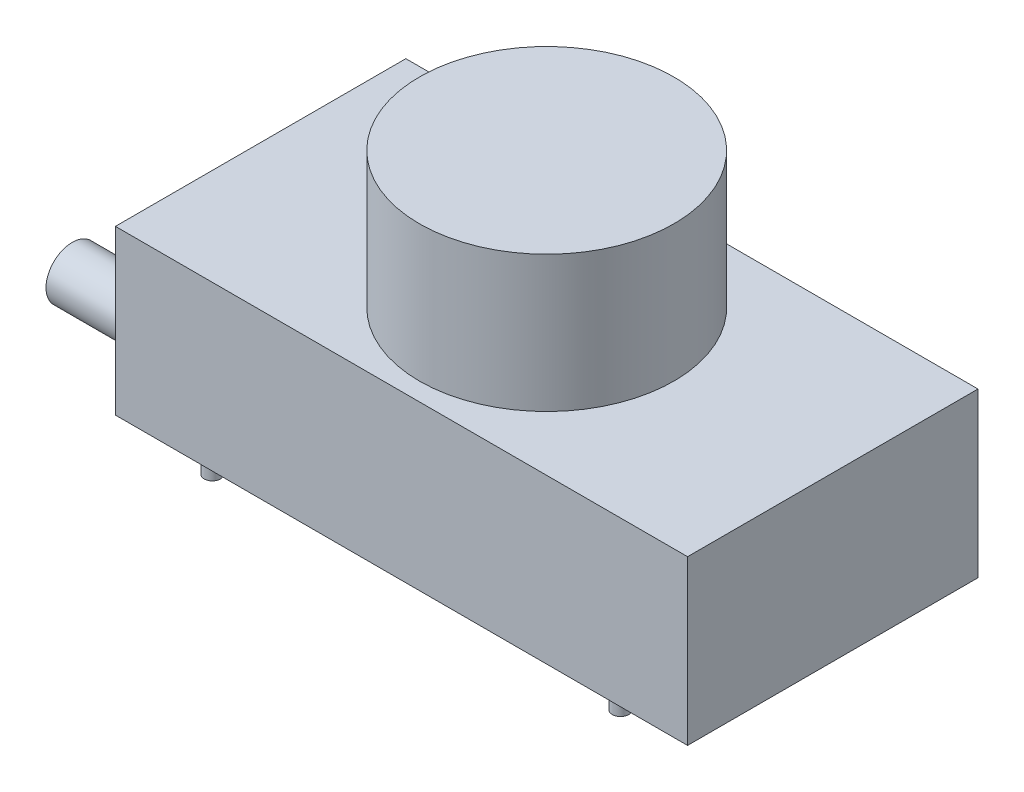
SolidWorks part; units mm, degrees
ref_plane "Front Plane" through (0, 0, 0) normal (0, 0, 1) x (1, 0, 0)
ref_plane "Top Plane" through (0, 0, 0) normal (0, 1, 0) x (1, 0, 0)
ref_plane "Right Plane" through (0, 0, 0) normal (1, 0, 0) x (0, 0, -1)
sketch "Sketch1" plane through (0, 0, 0) normal (0, 1, 0) x (1, 0, 0)
  line L1 (-52.5, -26.65) -> (52.5, -26.65)
  line L2 (-52.5, -26.65) -> (-52.5, 26.65)
  line L3 (-52.5, 26.65) -> (52.5, 26.65)
  line L4 (52.5, -26.65) -> (52.5, 26.65)
  line L5 (-52.5, -26.65) -> (52.5, 26.65) construction
  line L6 (-52.5, 26.65) -> (52.5, -26.65) construction
  point P0 (0, 0)
  dimension "D1" = 105
  dimension "D2" = 53.3
extrude "Boss-Extrude1" add sketch "Sketch1" along normal blind 30
sketch "Sketch2" plane through (-52.5, 0, 0) normal (-1, 0, 0) x (0, 0, 1)
  line L1 (-21.6019, 1.5708) -> (-14.012, 1.5708)
  line L2 (-21.6019, 1.5708) -> (-21.6019, 8.8239)
  line L3 (-21.6019, 8.8239) -> (-14.012, 8.8239)
  line L4 (-14.012, 1.5708) -> (-14.012, 8.8239)
  line L5 (-21.6019, 1.5708) -> (-14.012, 8.8239) construction
  line L6 (-21.6019, 8.8239) -> (-14.012, 1.5708) construction
  circle A0 centre (14.5675, 6.6027) radius 4.8187
  point P0 (-17.807, 5.1974)
extrude "Boss-Extrude2" add sketch "Sketch2" along normal blind 20
sketch "Sketch3" plane through (0, 30, 0) normal (0, 1, 0) x (1, 0, 0)
  circle A0 centre (0, 0) radius 23.3495
extrude "Boss-Extrude3" add sketch "Sketch3" along normal blind 25
sketch "Sketch4" plane through (0, 0, 0) normal (0, -1, 0) x (1, 0, 0)
  line L0 (52.5, -26.65) -> (-52.5, -26.65) construction
  line L1 (-38.5, -24.15) -> (43.6, -24.15) construction
  line L2 (-38.5, -24.15) -> (-38.5, 24.15) construction
  line L3 (-38.5, 24.15) -> (43.6, 24.15) construction
  line L4 (43.6, -24.15) -> (43.6, 24.15) construction
  line L5 (-52.5, 26.65) -> (52.5, 26.65) construction
  line L7 (-52.5, -26.65) -> (-52.5, 26.65) construction
  circle A0 centre (-37.2, 24.15) radius 1.5
  circle A1 centre (-38.5, -24.15) radius 1.5
  circle A2 centre (37.7, 24.15) radius 1.5
  circle A3 centre (43.6, -24.15) radius 1.5
  point P14 (44.7869, -24.15)
  point P15 (40.8602, 24.15)
  dimension "D6" = 3
  dimension "D1" = 2.5
  dimension "D2" = 2.5
  dimension "D3" = 1.3
  dimension "D4" = 74.9
  dimension "D5" = 82.1
  dimension "D7" = 14
extrude "Boss-Extrude4" add sketch "Sketch4" along normal blind 3
